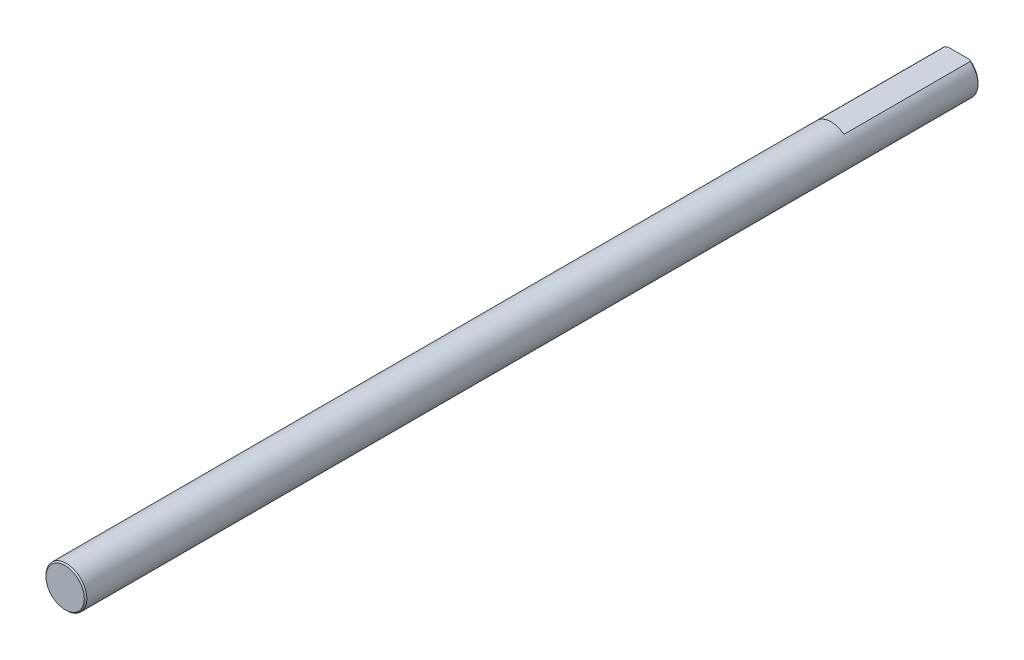
SolidWorks part; units mm, degrees
ref_plane "Front Plane" through (0, 0, 0) normal (0, 0, 1) x (1, 0, 0)
ref_plane "Top Plane" through (0, 0, 0) normal (0, 1, 0) x (1, 0, 0)
ref_plane "Right Plane" through (0, 0, 0) normal (1, 0, 0) x (0, 0, -1)
sketch "Sketch1" plane through (0, 0, 0) normal (0, 0, 1) x (1, 0, 0)
  circle A0 centre (0, 0) radius 1.6
  dimension "D1" = 3.2
extrude "Boss-Extrude1" add sketch "Sketch1" along normal blind 70
sketch "Sketch2" plane through (0, 0, 0) normal (1, 0, 0) x (0, 0, -1)
  line L0 (-10, 1.6) -> (-10, 1.25)
  line L1 (0, 1.6) -> (-70, 1.6) construction
  line L2 (-10, 1.25) -> (0, 1.25)
  line L3 (0, -1.6) -> (0, 1.6) construction
  line L4 (0, 1.25) -> (0, 1.6)
  line L5 (0, 1.6) -> (-10, 1.6)
  line L6 (-70, -1.6) -> (0, -1.6) construction
  dimension "D1" = 2.85
  dimension "D2" = 10
extrude "Cut-Extrude1" cut sketch "Sketch2" against normal through all and the other way through all
chamfer "Chamfer1" distance 0.1 angle 45 2 edges at (0, -1.6, 0) (1.6, 0, 70)
equation "\"D2@Sketch1\" = \"D1@Sketch1\" / 2.5"
